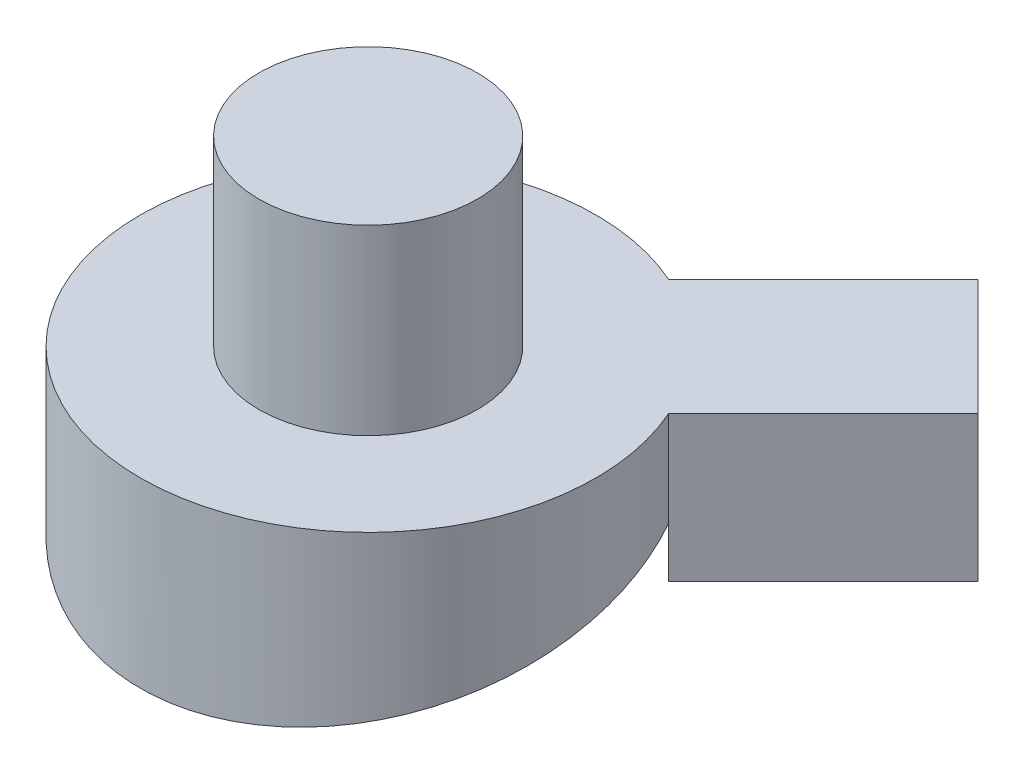
SolidWorks part; units mm, degrees
ref_plane "Front Plane" through (0, 0, 0) normal (0, 0, 1) x (1, 0, 0)
ref_plane "Top Plane" through (0, 0, 0) normal (0, 1, 0) x (1, 0, 0)
ref_plane "Right Plane" through (0, 0, 0) normal (1, 0, 0) x (0, 0, -1)
sketch "Sketch2" plane through (0, 0, 0) normal (0, 1, 0) x (1, 0, 0)
  circle A0 centre (0, 0) radius 62.5
  dimension "D1" = 125
extrude "Boss-Extrude1" add sketch "Sketch2" along normal blind 50
sketch "Sketch3" plane through (0, 0, 0) normal (1, 0, 0) x (0, 0, -1)
  line L0 (-62.5, 0) -> (62.5, 34)
  line L1 (62.5, 0) -> (62.5, 50) construction
  line L2 (62.5, 34) -> (62.5, 0)
  line L3 (62.5, 0) -> (-62.5, 0)
  line L4 (62.5, 50) -> (-62.5, 50) construction
  dimension "D1" = 16
extrude "Cut-Extrude1" cut sketch "Sketch3" against normal through all both and the other way through all
sketch "Sketch4" plane through (0, 50, 0) normal (0, 1, 0) x (1, 0, 0)
  circle A0 centre (0, 0) radius 30
  dimension "D1" = 60
extrude "Boss-Extrude2" add sketch "Sketch4" along normal blind 50
sketch "Sketch5" plane through (0, 15.8289, 4.3055) normal (0, -0.9649, -0.2625) x (1, 0, 0)
  circle A0 centre (0, -4.4619) radius 50
  ellipse E0 centre (0, -4.4619) end of major axis (0, 60.3089) minor radius 62.5 construction
  dimension "D1" = 100
extrude "Cut-Extrude2" cut sketch "Sketch5" against normal blind 10 and the other way through all
sketch "Sketch7" plane through (0, 0, 0) normal (1, 0, 0) x (0, 0, -1)
  line L0 (-50.8717, 13.5262) -> (45.6224, 39.7726) construction
  line L1 (-50.8717, 13.5262) -> (45.6224, 39.7726) construction
  line L2 (-50.8717, 13.5262) -> (-1.2737, 14.0627)
  line L3 (-1.2737, 14.0627) -> (0.6562, 14.5876)
  line L4 (0.6562, 14.5876) -> (-2.6246, 26.6494)
  line L5 (-2.6246, 26.6494) -> (-50.8717, 13.5262)
  point P2 (-9.6013, 10.9729)
  point P6 (-3.5158, 13.5262)
  point P7 (0, 0)
  point P8 (-3.0028, 13.5262)
  dimension "D1" = 12.5
  dimension "D2" = 2
revolve "Revolve1" add sketch "Sketch7" angle 360 about L4
sketch "Sketch8" plane through (0, 50, 0) normal (0, 1, 0) x (1, 0, 0)
  line L0 (25.3212, 57.141) -> (67.7476, 99.5674)
  line L1 (67.7476, 99.5674) -> (99.5674, 67.7476)
  line L2 (99.5674, 67.7476) -> (57.141, 25.3212)
  line L3 (0, -1000) -> (0, 49000) construction
  line L4 (0, 0) -> (106.6433, 106.6433) construction
  circle A0 centre (0, 0) radius 62.5 construction
  arc A1 (57.141, 25.3212) -> (25.3212, 57.141) centre (0, 0) ccw
  arc A2 (0, 62.5) -> (0, -62.5) centre (0, 0) ccw construction
  arc A3 (25.3212, 57.141) -> (0, 62.5) centre (0, 0) ccw construction
  arc A4 (0, -62.5) -> (57.141, 25.3212) centre (0, 0) ccw construction
  point P10 (83.6575, 83.6575)
  point P14 (0, 0)
  dimension "D1" = 45
  dimension "D2" = 45
  dimension "D3" = 45
  dimension "D4" = 60
extrude "Boss-Extrude3" add sketch "Sketch8" against normal blind 40
